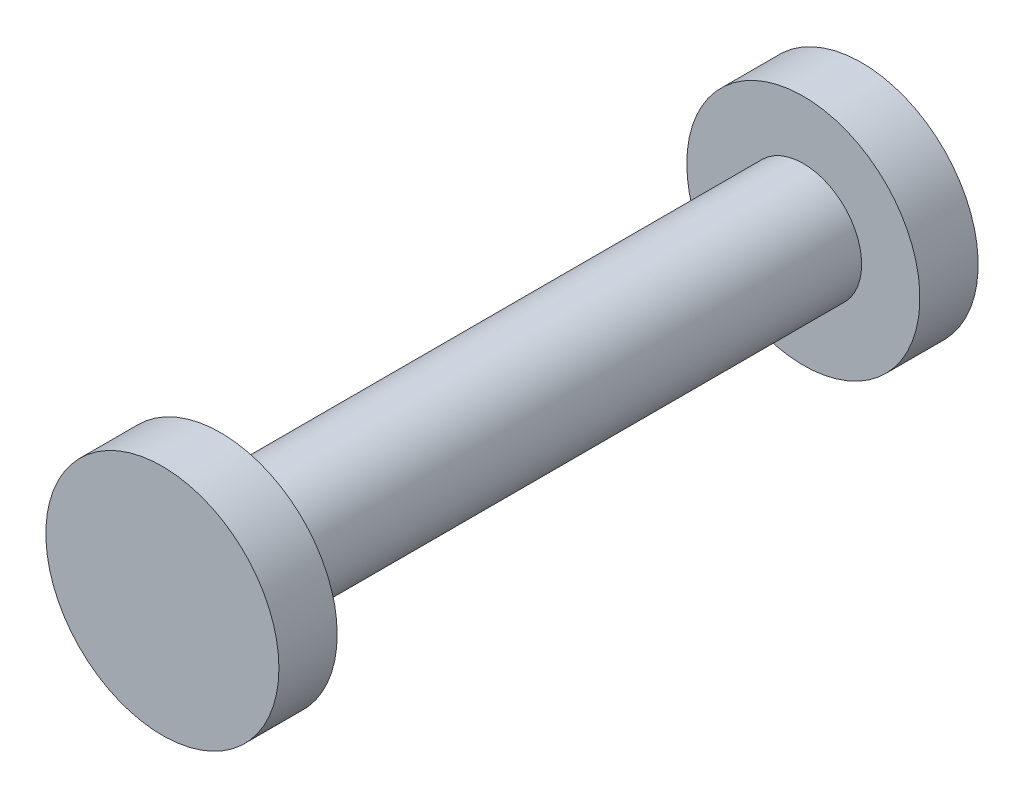
SolidWorks part; units mm, degrees
ref_plane "Front Plane" through (0, 0, 0) normal (0, 0, 1) x (1, 0, 0)
ref_plane "Top Plane" through (0, 0, 0) normal (0, 1, 0) x (1, 0, 0)
ref_plane "Right Plane" through (0, 0, 0) normal (1, 0, 0) x (0, 0, -1)
sketch "Sketch2" plane through (0, 0, 0) normal (0, 0, 1) x (1, 0, 0)
  circle A0 centre (0, 0) radius 5
  dimension "D1" = 10
extrude "Boss-Extrude1" add sketch "Sketch2" along normal blind 50
sketch "Sketch3" plane through (0, 0, 0) normal (0, 0, -1) x (-1, 0, 0)
  circle A0 centre (0, 0) radius 10
extrude "Boss-Extrude2" add sketch "Sketch3" along normal blind 5
sketch "Sketch4" plane through (0, 0, 50) normal (0, 0, 1) x (1, 0, 0)
  circle A0 centre (0, 0) radius 10
  dimension "D1" = 20
extrude "Boss-Extrude3" add sketch "Sketch4" along normal blind 5
